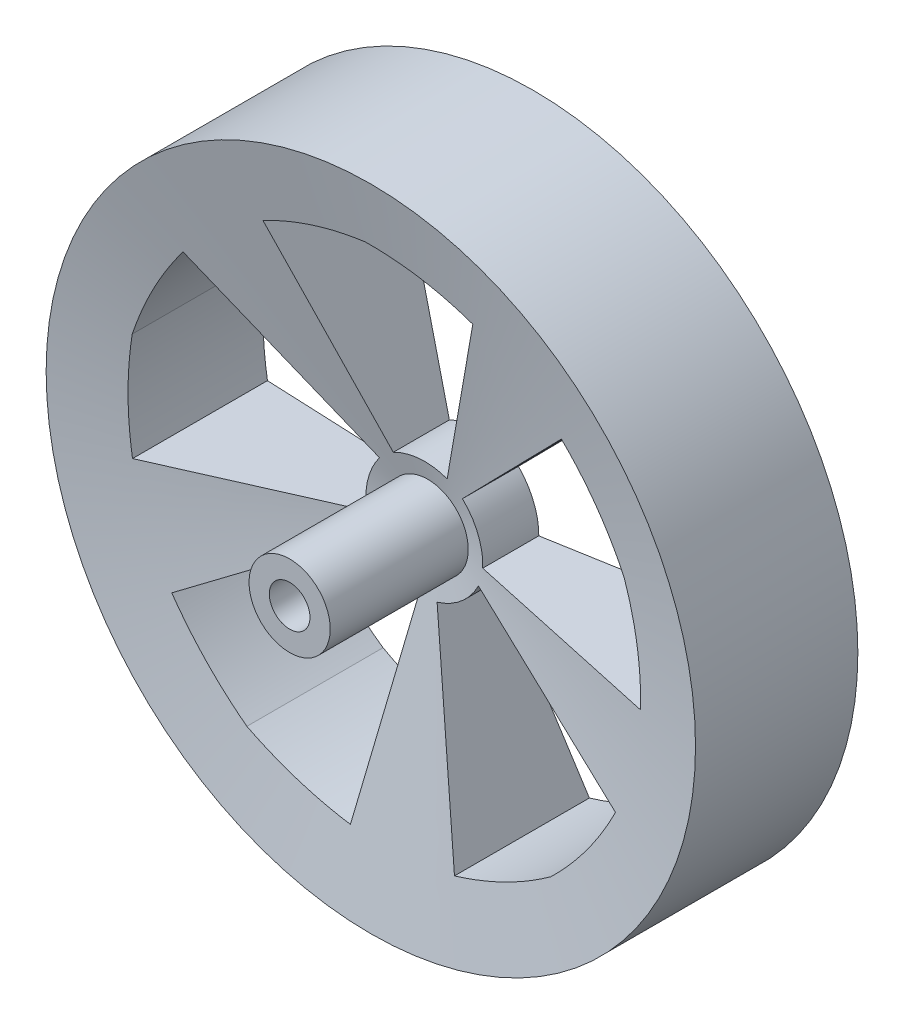
SolidWorks part; units mm, degrees
ref_plane "Front Plane" through (0, 0, 0) normal (0, 0, 1) x (1, 0, 0)
ref_plane "Top Plane" through (0, 0, 0) normal (0, 1, 0) x (1, 0, 0)
ref_plane "Right Plane" through (0, 0, 0) normal (1, 0, 0) x (0, 0, -1)
sketch "Sketch2" plane through (0, 0, 0) normal (1, 0, 0) x (0, 0, -1)
  line L0 (-1.9474, 0) -> (13.4211, 0) construction
  line L1 (-0.9474, 0) -> (3.0526, 20)
  line L2 (3.0526, 20) -> (-6.9474, 20)
  line L4 (-2.9474, 0) -> (-0.9474, 0)
  line L5 (-2.9474, 0) -> (-6.9474, 20)
  dimension "D1" = 10
  dimension "D2" = 1
  dimension "D3" = 20
revolve "Revolve2" add sketch "Sketch2" angle 360 about L0
ref_plane "Plane2" through (0, 0, 6.9474) normal (0, 0, 1) x (1, 0, 0)
sketch "Sketch3" plane through (0, 0, 6.9474) normal (0, 0, 1) x (1, 0, 0)
  line L0 (-1.3956, 19.5018) -> (0, 0) construction
  line L1 (0, 0) -> (1.4276, -19.949) construction
  line L3 (1.4276, 3.3418) -> (5.4374, 14.8129)
  line L4 (3.6194, -0.3251) -> (15.7681, -0.5939)
  line L6 (-1.889, 3.1044) -> (-7.4914, 13.8876)
  line L7 (2.3688, 2.7558) -> (10.893, 11.4162)
  line L8 (0.8093, -3.5427) -> (4.3078, -15.1799)
  line L9 (3.3529, -1.4012) -> (14.2236, -6.832)
  line L10 (-3.1192, -1.8644) -> (-13.1057, -8.7878)
  line L11 (-0.2965, -3.6218) -> (-2.1023, -15.6386)
  line L12 (-2.7371, 2.3904) -> (-12.4076, 9.7487)
  line L13 (-3.5362, -0.8372) -> (-15.5229, -2.8332)
  circle A0 centre (0, 0) radius 20 construction
  arc A1 (5.4374, 14.8129) -> (-1.14, 15.9293) centre (-1.14, -4.0036) ccw
  arc A2 (-7.4914, 13.8876) -> (-1.14, 15.9293) centre (1.6985, -3.8004) cw
  arc A3 (-1.889, 3.1044) -> (1.4276, 3.3418) centre (0.0441, -0.6162) cw
  arc A4 (2.3688, 2.7558) -> (3.6194, -0.3251) centre (-0.5724, -0.2324) cw
  arc A5 (15.7681, -0.5939) -> (14.7974, 6.0066) centre (-4.1599, -0.153) ccw
  arc A6 (10.893, 11.4162) -> (14.7974, 6.0066) centre (-3.0896, -2.7897) cw
  arc A7 (3.3529, -1.4012) -> (0.8093, -3.5427) centre (-0.3979, 0.4726) cw
  arc A8 (4.3078, -15.1799) -> (10.2853, -12.217) centre (-1.431, 3.909) ccw
  arc A9 (14.2236, -6.832) -> (10.2853, -12.217) centre (-3.6079, 2.0763) cw
  arc A10 (-0.2965, -3.6218) -> (-3.1192, -1.8644) centre (0.3265, 0.5244) cw
  arc A11 (-13.1057, -8.7878) -> (-8.4408, -13.5571) centre (3.2755, 2.5689) ccw
  arc A12 (-2.1023, -15.6386) -> (-8.4408, -13.5571) centre (0.8598, 4.073) cw
  arc A13 (-3.5362, -0.8372) -> (-2.7371, 2.3904) centre (0.5997, -0.1485) cw
  arc A14 (-12.4076, 9.7487) -> (-15.502, 3.8383) centre (3.4554, -2.3214) ccw
  arc A15 (-15.5229, -2.8332) -> (-15.502, 3.8383) centre (4.1393, 0.4409) cw
  point P49 (0, 0)
  dimension "D1" = 5
extrude "Cut-Extrude1" cut sketch "Sketch3" against normal through all
sketch "Sketch4" plane through (0, 0, 6.9474) normal (0, 0, 1) x (1, 0, 0)
  circle A0 centre (0, 0) radius 2.5
  dimension "D1" = 5
extrude "Boss-Extrude1" add sketch "Sketch4" along normal blind 5 and the other way up to body (5 mm away) separate body
sketch "Sketch5" plane through (0, 0, 11.9474) normal (0, 0, 1) x (1, 0, 0)
  circle A0 centre (0, 0) radius 1.25
  dimension "D1" = 2.5
extrude "Cut-Extrude2" cut sketch "Sketch5" against normal blind 5 contours A0
